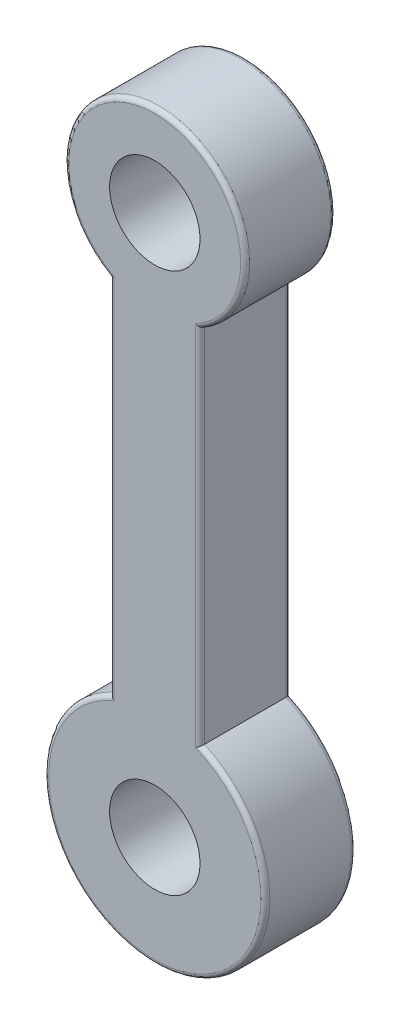
SolidWorks part; units mm, degrees
material "Plain Carbon Steel"
ref_plane "Plan de face" through (0, 0, 0) normal (0, 0, 1) x (1, 0, 0)
ref_plane "Plan de dessus" through (0, 0, 0) normal (0, 1, 0) x (1, 0, 0)
ref_plane "Plan de droite" through (0, 0, 0) normal (1, 0, 0) x (0, 0, -1)
sketch "Esquisse1" plane through (0, 0, 0) normal (0, 0, 1) x (1, 0, 0)
  line L1 (-10, -17.3205) -> (-10, -97.3205)
  line L2 (10, -17.3205) -> (10, -97.3205)
  circle A0 centre (0, 0) radius 10
  arc A1 (10, -17.3205) -> (-10, -17.3205) centre (0, 0) ccw
  circle A2 centre (0, -119.641) radius 10
  arc A3 (-10, -97.3205) -> (10, -97.3205) centre (0, -119.641) ccw
  point P7 (-10, 0)
  point P8 (-10, -70)
  point P9 (10, 0)
  point P10 (10, -70)
  dimension "D1" = 80
  dimension "D2" = 80
extrude "Boss.-Extru.1" add sketch "Esquisse1" along normal blind 20
fillet "Congé2" radius 1 8 edges at (0, -144.0992, 20) (-10, -57.3205, 20) (0, 20, 20) (10, -57.3205, 20) (10, -57.3205, 0) (0, -144.0992, 0) (-10, -57.3205, 0) (0, 20, 0)
sketch "Sketch1" plane through (0, 0, 20) normal (0, 0, 1) x (1, 0, 0)
  point P0 (0, -119.641)
sketch "Sketch2" plane through (0, 0, 0) normal (0, 0, -1) x (-1, 0, 0)
  point P0 (0, 0)
  point P1 (0, -119.641)
sketch "Sketch3" plane through (0, 0, 20) normal (0, 0, 1) x (1, 0, 0)
  point P0 (0, 0)
